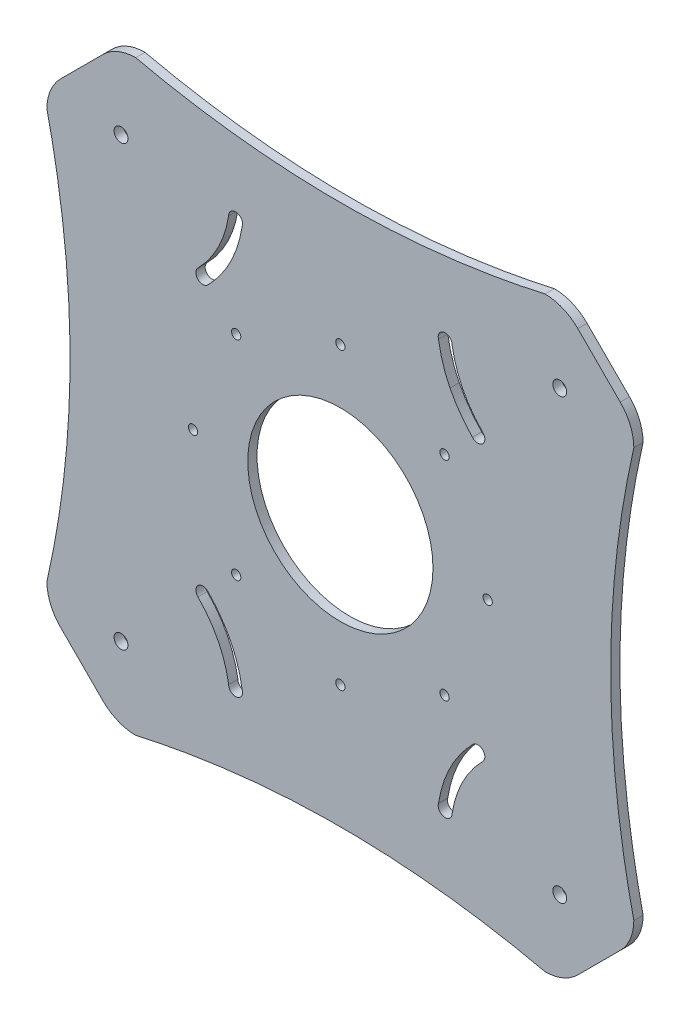
SolidWorks part; units mm, degrees
material "Hexcel AS4C (3000 Filaments)"
ref_plane "Front Plane" through (0, 0, 0) normal (0, 0, 1) x (1, 0, 0)
ref_plane "Top Plane" through (0, 0, 0) normal (0, 1, 0) x (1, 0, 0)
ref_plane "Right Plane" through (0, 0, 0) normal (1, 0, 0) x (0, 0, -1)
sketch "Sketch1" plane through (0, 0, 0) normal (0, 0, 1) x (1, 0, 0)
  line L0 (-113.7048, 0) -> (47.3762, 0) construction
  line L1 (47.3762, 47.3762) -> (47.3762, 0) construction
  line L2 (47.3762, 0) -> (47.3762, -47.3762) construction
  line L3 (0, 0) -> (59.397, 59.397) construction
  line L4 (22.6274, 43.8406) -> (25.8154, 37.4647) construction
  line L5 (26.163, 36.7696) -> (16.7377, 32.0569) construction
  line L6 (26.5105, 36.0744) -> (29.6985, 29.6985) construction
  line L7 (0, 0) -> (0, -74.2241) construction
  line L8 (0, -74.2241) -> (0, 77.8962) construction
  line L9 (51.2756, 60.4472) -> (60.4472, 51.2756)
  line L10 (60.4472, -51.2756) -> (51.2756, -60.4472)
  line L11 (-51.2756, -60.4472) -> (-60.4472, -51.2756)
  line L12 (-60.4472, 51.2756) -> (-51.2756, 60.4472)
  line L13 (51.2756, -60.4472) -> (60.4472, -51.2756)
  line L14 (-47.3762, 47.3762) -> (29.6985, -29.6985) construction
  line L15 (63.3762, 0) -> (58.3762, 0) construction
  circle A0 centre (0, 0) radius 20
  circle A1 centre (47.3762, 47.3762) radius 1.5
  circle A2 centre (47.3762, -47.3762) radius 1.5
  circle A3 centre (22.5, 22.5) radius 1
  arc A4 (28.5165, 28.7749) -> (30.7591, 30.7591) centre (29.6985, 29.6985) ccw
  circle A5 centre (31.8198, 0) radius 1
  circle A6 centre (22.5, -22.5) radius 1
  circle A7 centre (0, -31.8198) radius 1
  circle A8 centre (-22.5, -22.5) radius 1
  circle A9 centre (-31.8198, 0) radius 1
  circle A10 centre (-22.5, 22.5) radius 1
  circle A11 centre (0, 31.8198) radius 1
  circle A12 centre (47.3762, -47.3762) radius 1.5
  circle A13 centre (-47.3762, -47.3762) radius 1.5
  circle A14 centre (-47.3762, 47.3762) radius 1.5
  arc A15 (22.8912, 42.364) -> (23.2982, 42.499) centre (22.6274, 43.8406) ccw
  arc A16 (26.3629, 36.8549) -> (26.3497, 36.8812) centre (25.0155, 36.1958) ccw
  arc A17 (24.1274, 43.8406) -> (21.1918, 43.4059) centre (22.6274, 43.8406) ccw
  arc A18 (23.6736, 35.5255) -> (23.6738, 35.525) centre (25.0155, 36.1958) ccw
  arc A19 (-24.1274, 43.8406) -> (-21.1918, 43.4059) centre (-22.6274, 43.8406) cw
  arc A20 (-28.5165, 28.7749) -> (-30.7591, 30.7591) centre (-29.6985, 29.6985) cw
  arc A21 (-28.5165, -28.7749) -> (-30.7591, -30.7591) centre (-29.6985, -29.6985) ccw
  arc A22 (-24.1274, -43.8406) -> (-21.1918, -43.4059) centre (-22.6274, -43.8406) ccw
  arc A23 (24.1274, -43.8406) -> (21.1918, -43.4059) centre (22.6274, -43.8406) cw
  arc A24 (28.5165, -28.7749) -> (30.7591, -30.7591) centre (29.6985, -29.6985) cw
  arc A25 (63.3762, 44.2046) -> (60.4472, 51.2756) centre (53.3762, 44.2046) ccw
  arc A26 (51.2756, 60.4472) -> (44.2046, 63.3762) centre (44.2046, 53.3762) ccw
  arc A27 (63.3762, -44.2046) -> (60.4472, -51.2756) centre (53.3762, -44.2046) cw
  arc A28 (51.2756, -60.4472) -> (44.2046, -63.3762) centre (44.2046, -53.3762) cw
  arc A29 (60.4472, -51.2756) -> (63.3762, -44.2046) centre (53.3762, -44.2046) ccw
  arc A30 (44.2046, -63.3762) -> (51.2756, -60.4472) centre (44.2046, -53.3762) ccw
  arc A31 (-51.2756, -60.4472) -> (-44.2046, -63.3762) centre (-44.2046, -53.3762) ccw
  arc A32 (-63.3762, -44.2046) -> (-60.4472, -51.2756) centre (-53.3762, -44.2046) ccw
  arc A33 (-60.4472, 51.2756) -> (-63.3762, 44.2046) centre (-53.3762, 44.2046) ccw
  arc A34 (-44.2046, 63.3762) -> (-51.2756, 60.4472) centre (-44.2046, 53.3762) ccw
  spline S0 degree 2 poles (-24.1274, 43.8406) (-25.3624, 36.2517) (-30.7591, 30.7591) knots 0 0 0 1 1 1
  spline S1 degree 2 poles (24.1274, 43.8406) (25.3624, 36.2517) (30.7591, 30.7591) knots 0 0 0 1 1 1
  spline S2 degree 2 poles (21.1274, 43.8406) (22.3834, 34.9061) (28.761, 28.5275) knots 0 0 0 1 1 1
  spline S3 degree 2 poles (-21.1274, 43.8406) (-22.3834, 34.9061) (-28.761, 28.5275) knots 0 0 0 1 1 1
  spline S4 degree 2 poles (-24.1274, -43.8406) (-25.3624, -36.2517) (-30.7591, -30.7591) knots 0 0 0 1 1 1
  spline S5 degree 2 poles (-21.1274, -43.8406) (-22.3834, -34.9061) (-28.761, -28.5275) knots 0 0 0 1 1 1
  spline S6 degree 2 poles (24.1274, -43.8406) (25.3624, -36.2517) (30.7591, -30.7591) knots 0 0 0 1 1 1
  spline S7 degree 2 poles (21.1274, -43.8406) (22.3834, -34.9061) (28.761, -28.5275) knots 0 0 0 1 1 1
  spline S8 degree 2 poles (63.3762, 44.2046) (53.3762, 0) (63.3762, -44.2046) knots 0 0 0 1 1 1
  spline S9 degree 2 poles (44.2046, -63.3762) (0, -53.3762) (-44.2046, -63.3762) knots 0 0 0 1 1 1
  spline S10 degree 2 poles (-63.3762, -44.2046) (-53.3762, 0) (-63.3762, 44.2046) knots 0 0 0 1 1 1
  spline S11 degree 2 poles (-44.2046, 63.3762) (0, 53.3762) (44.2046, 63.3762) knots 0 0 0 1 1 1
  point P31 (0, 0)
  point P38 (0, 0)
  point P93 (63.3762, 48.3467)
  point P96 (48.3467, 63.3762)
  point P125 (0, 0)
  point P126 (0, 0)
  point P134 (0, 0)
  dimension "D1" = 25
  dimension "D2" = 3
  dimension "D4" = 31.8198
  dimension "D6" = 40
  dimension "D11" = 12
  dimension "D12" = 16
  dimension "D14" = 10
  dimension "D15" = 10
  dimension "D7" = 2
  dimension "D3" = 45
  dimension "D5" = 8
  dimension "D9" = 25
  dimension "D10" = 25
  dimension "D13" = 16
  dimension "D16" = 5
  dimension "D8" = 4
  dimension "D17" = 4
extrude "Boss-Extrude1" add sketch "Sketch1" along normal blind 2
